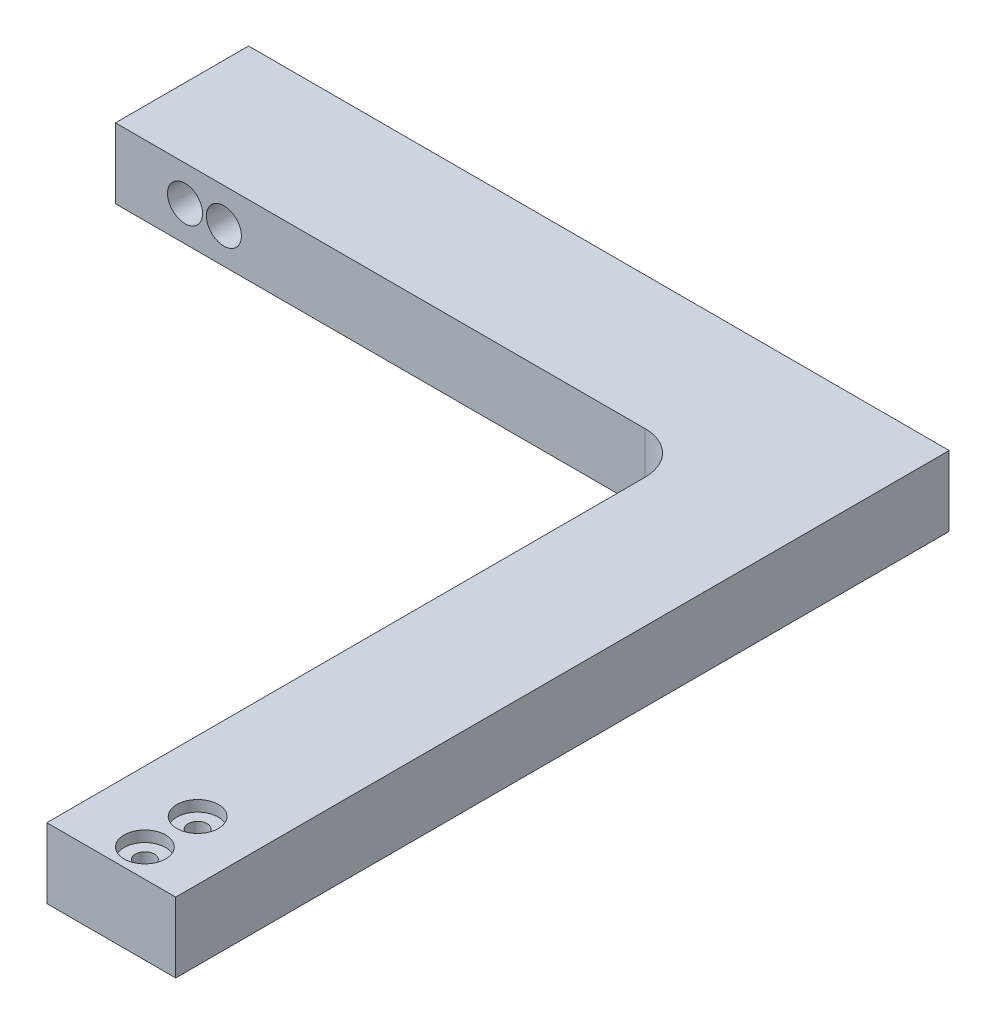
SolidWorks part; units mm, degrees
ref_plane "Front Plane" through (0, 0, 0) normal (0, 0, 1) x (1, 0, 0)
ref_plane "Top Plane" through (0, 0, 0) normal (0, 1, 0) x (1, 0, 0)
ref_plane "Right Plane" through (0, 0, 0) normal (1, 0, 0) x (0, 0, -1)
sketch "Sketch1" plane through (0, 0, 0) normal (0, 1, 0) x (1, 0, 0)
  line L0 (-12.7, 39.878) -> (-116.332, 39.878)
  line L2 (-12.7, 39.878) -> (-12.7, -76.2)
  line L3 (-12.7, -76.2) -> (10.668, -76.2)
  line L4 (10.668, 64.008) -> (10.668, -76.2)
  line L5 (-10.7534, 76.8099) -> (10.668, -76.2) construction
  line L6 (-12.7, -76.2) -> (10.668, 64.008) construction
  line L7 (10.668, 64.008) -> (-116.332, 64.008)
  line L10 (-116.332, 64.008) -> (-116.332, 39.878)
  point P0 (0, 0)
extrude "Boss-Extrude1" add sketch "Sketch1" along normal blind 12.7
fillet "Fillet1" radius 7.62 1 edges at (-12.7, 6.35, -39.878)
sketch "Sketch2" plane through (0, 12.7, 0) normal (0, 1, 0) x (1, 0, 0)
  line L2 (0, -71.12) -> (0, -54.61)
hole_wizard "CBORE for #5 Binding Head Machine Screw1" positions "Sketch7" profile "Sketch8" counterbore size "#5" standard "ANSI Inch" end condition up to next
sketch "Sketch7" plane through (0, 12.7, 0) normal (0, 1, 0) x (1, 0, 0)
  line L0 (0, -71.12) -> (0, -54.61) construction
  point P0 (0, -71.12)
  point P3 (0, -61.5609)
sketch "Sketch8" plane through (0, 12.7, 71.12) normal (1, 0, 0) x (0, 0, 1)
  line L0 (0, 0) -> (0, 12.7)
  line L1 (0, 12.7) -> (1.7272, 12.7)
  line L3 (1.7272, 12.7) -> (1.7272, 1.9812)
  line L4 (1.7272, 1.9812) -> (3.7706, 1.9812)
  line L5 (3.7706, 1.9812) -> (3.7706, 0)
  line L7 (3.7706, 0) -> (0, 0)
  line L11 (0, -6.35) -> (0, 107.95) construction
  dimension "Thru Hole Dia." = 3.4544
  dimension "Thru Hole Depth" = 12.7
  dimension "C'Bore Dia." = 7.5413
  dimension "C'Bore Depth" = 1.9812
sketch "Sketch9" plane through (0, 0, -64.008) normal (0, 0, -1) x (-1, 0, 0)
  line L0 (116.332, 6.35) -> (103.7182, 6.35)
  line L1 (116.332, 12.7) -> (116.332, 0) construction
  line L2 (103.7182, 6.35) -> (99.2732, 6.35)
hole_wizard "1/4 (0.25) Diameter Hole2" positions "Sketch17" profile "Sketch18" hole size "1/4" standard "ANSI Inch" end condition up to next
sketch "Sketch17" plane through (0, 0, -64.008) normal (0, 0, -1) x (-1, 0, 0)
  point P0 (103.7182, 6.35)
  point P3 (96.6728, 6.35)
sketch "Sketch18" plane through (-103.7182, 6.35, -64.008) normal (1, 0, 0) x (0, 1, 0)
  line L0 (0, 0) -> (0, 24.13)
  line L1 (0, 24.13) -> (3.175, 24.13)
  line L2 (3.175, 24.13) -> (3.175, 0)
  line L5 (3.175, 0) -> (0, 0)
  line L11 (0, -6.35) -> (0, 107.95) construction
  dimension "Thru Hole Dia." = 6.35
  dimension "Thru Hole Depth" = 24.13
